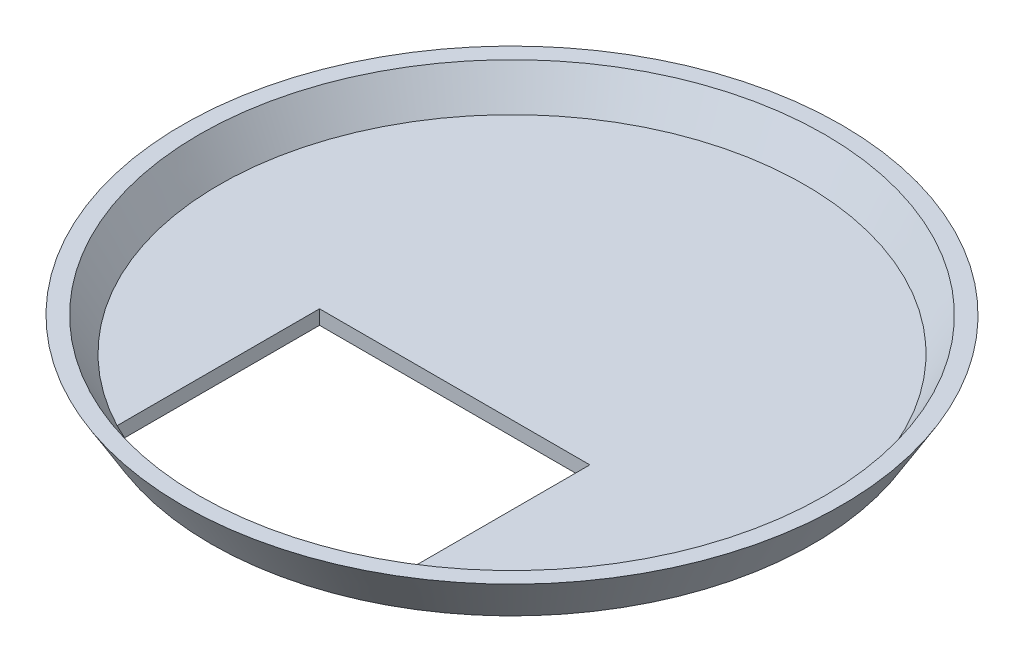
SolidWorks part; units mm, degrees
ref_plane "Front Plane" through (0, 0, 0) normal (0, 0, 1) x (1, 0, 0)
ref_plane "Top Plane" through (0, 0, 0) normal (0, 1, 0) x (1, 0, 0)
ref_plane "Right Plane" through (0, 0, 0) normal (1, 0, 0) x (0, 0, -1)
sketch "Sketch1" plane through (0, 0, 0) normal (0, 0, 1) x (1, 0, 0)
  line L0 (0, 0) -> (63, 0)
  line L1 (63, 0) -> (69, 10)
  line L6 (0, 3) -> (61.3014, 3)
  line L7 (61.3014, 3) -> (65.5014, 10)
  line L8 (69, 10) -> (65.5014, 10)
  line L9 (0, 0) -> (0, 3)
  line L10 (61.3014, 3) -> (66.4275, 11.5435) construction
  dimension "D1" = 69
  dimension "D2" = 63
  dimension "D3" = 10
  dimension "D4" = 3
revolve "Revolve1" add sketch "Sketch1" angle 360 about L9
sketch "Sketch2" plane through (0, 3, 0) normal (0, 1, 0) x (1, 0, 0)
  line L0 (-28.3, -12) -> (-28.3, -54.3781)
  line L1 (-28.3, -12) -> (28.3, -12)
  line L5 (28.3, -12) -> (28.3, -54.3781)
  arc A0 (-28.3, -54.3781) -> (28.3, -54.3781) centre (0, 0) ccw
  circle A3 centre (0, 0) radius 61.3014 construction
  dimension "D2" = 28.3
  dimension "D1" = 56.6
  dimension "D4" = 12
extrude "Cut-Extrude1" cut sketch "Sketch2" against normal through all
